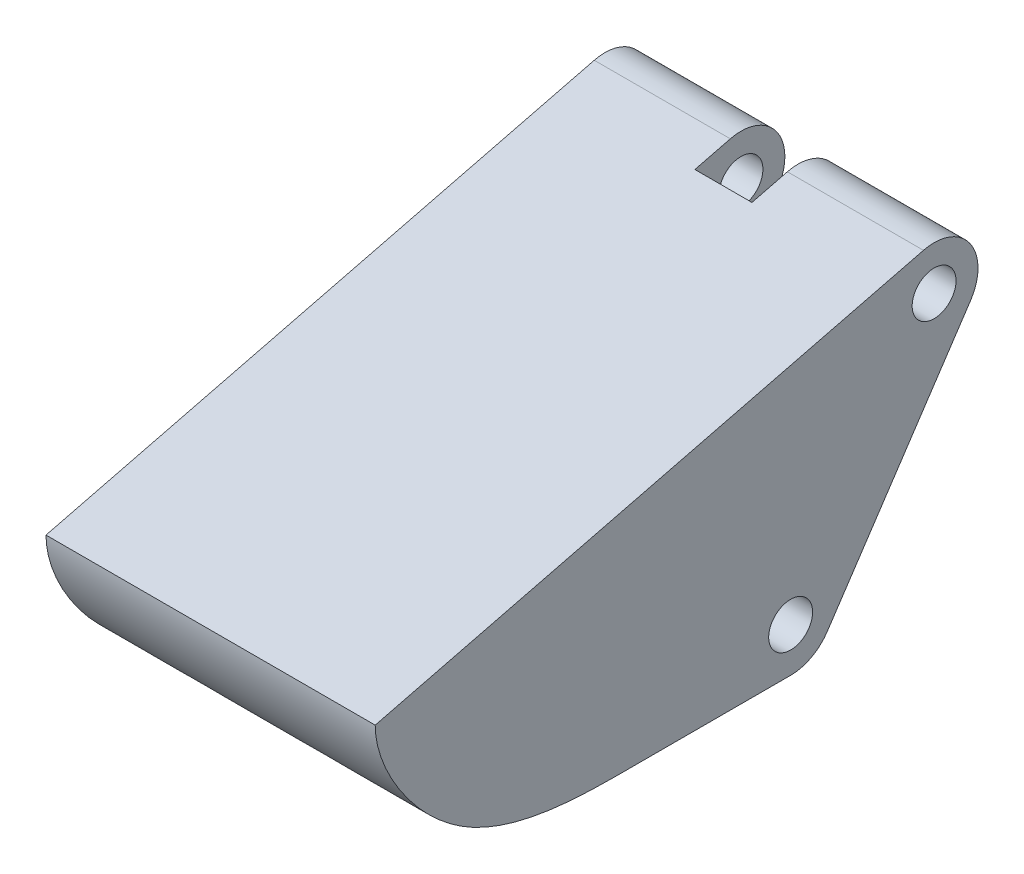
SolidWorks part; units mm, degrees
ref_plane "Front Plane" through (0, 0, 0) normal (0, 0, 1) x (1, 0, 0)
ref_plane "Top Plane" through (0, 0, 0) normal (0, 1, 0) x (1, 0, 0)
ref_plane "Right Plane" through (0, 0, 0) normal (1, 0, 0) x (0, 0, -1)
sketch "Sketch2" plane through (0, 0, 0) normal (1, 0, 0) x (0, 0, -1)
  line L0 (-5.0188, 6.2453) -> (-30, 0)
  line L1 (-18, -7.5) -> (-10, -7.5)
  line L5 (0, 7.5) -> (0, -7.5) construction
  line L6 (0, -7.5) -> (-10, -7.5) construction
  line L7 (-2.8696, 3.1956) -> (-9.4063, -6.6094)
  line L8 (-11.0704, -7.5) -> (-18, -7.5)
  line L9 (-30, 0) -> (0, 0) construction
  arc A0 (-9.4063, -6.6094) -> (-11.0704, -7.5) centre (-11.0704, -5.5) cw
  arc A1 (-2.8696, 3.1956) -> (-5.0188, 6.2453) centre (-4.5337, 4.305) ccw
  circle A2 centre (-4.5337, 4.305) radius 1
  circle A3 centre (-11.0704, -5.5) radius 1
  spline S0 degree 3 poles (-30, 0) (-30, -1.862) (-26.2969, -7.6709) (-20.2336, -7.5) (-18, -7.5) knots 0 0 0 0 0.469763 1 1 1 1
  point P0 (0, 0)
  point P13 (0, 0)
  dimension "D5" = 2
  dimension "D6" = 8
  dimension "D8" = 2
  dimension "D9" = 2
  dimension "D1" = 15
  dimension "D2" = 30
  dimension "D3" = 10
  dimension "D4" = 8
  dimension "D7" = 6
extrude "Boss-Extrude1" add sketch "Sketch2" along normal mid plane 15 contours L0 S0 L1 A0 L7 A1
ref_plane "Plane1" through (0, 6.305, 0) normal (0, 1, 0) x (1, 0, 0)
sketch "Sketch4" plane through (0, 6.305, 0) normal (0, 1, 0) x (1, 0, 0)
  line L0 (7.5, -2.5337) -> (-7.5, -2.5337) construction
  line L1 (1.3, -6.6337) -> (-1.3, -6.6337)
  line L2 (1.3, -6.6337) -> (1.3, -2.5337)
  line L3 (1.3, -2.5337) -> (-1.3, -2.5337)
  line L4 (-1.3, -6.6337) -> (-1.3, -2.5337)
  line L5 (1.3, -6.6337) -> (-1.3, -2.5337) construction
  line L6 (1.3, -2.5337) -> (-1.3, -6.6337) construction
  line L9 (-7.5, -3.7762) -> (7.5, -3.7762) construction
  line L10 (-7.5, -2.5337) -> (-7.5, -5.0188) construction
  line L11 (7.5, -5.0188) -> (7.5, -2.5337) construction
  point P0 (0, -4.5837)
  point P13 (0, -3.7762)
  dimension "D1" = 4.1
  dimension "D2" = 2.6
extrude "Cut-Extrude1" cut sketch "Sketch4" against normal blind 15
sketch "Sketch5" plane through (0, -7.5, 0) normal (0, -1, 0) x (1, 0, 0)
  line L1 (5, 7.0704) -> (-5, 7.0704)
  line L2 (5, 7.0704) -> (5, 14.0704)
  line L4 (-5, 7.0704) -> (-5, 14.0704)
  line L5 (5, 7.0704) -> (-5, 14.0704) construction
  line L6 (5, 14.0704) -> (-5, 7.0704) construction
  line L7 (7.5, 11.0704) -> (-7.5, 11.0704) construction
  arc A0 (-5, 14.0704) -> (5, 14.0704) centre (0, 10.7537) cw
  point P0 (0, 10.5704)
  dimension "D4" = 6
  dimension "D1" = 3
  dimension "D2" = 7
  dimension "D3" = 10
  dimension "D5" = 10
extrude "Cut-Extrude3" cut sketch "Sketch5" against normal blind 4
